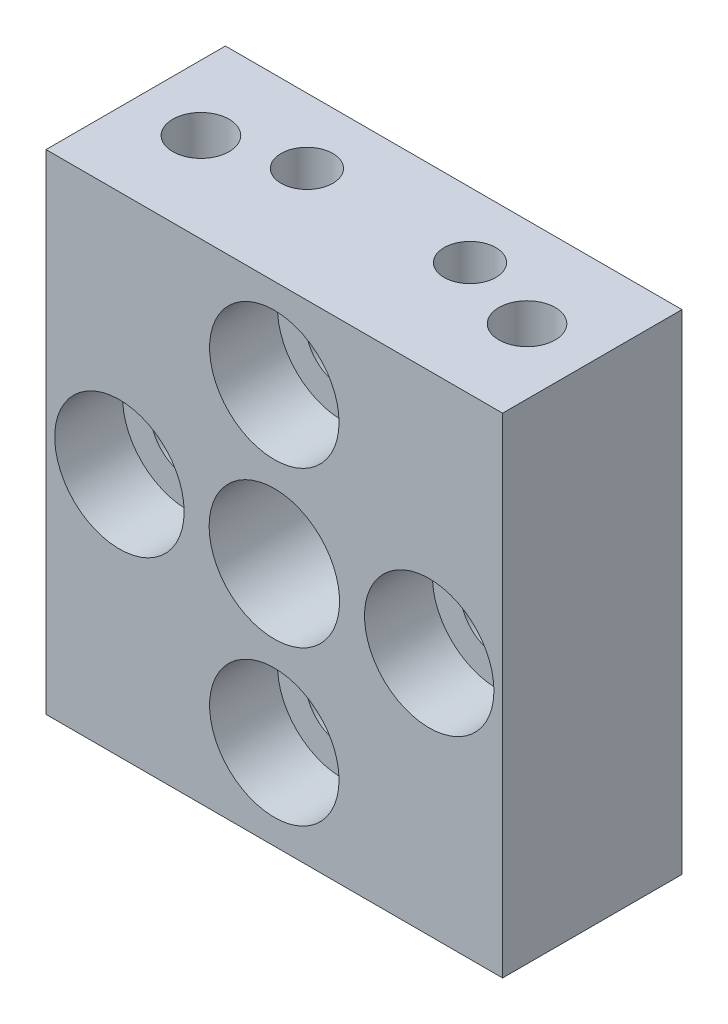
SolidWorks part; units mm, degrees
material "AISI 316 Annealed Stainless Steel Bar (SS)"
ref_plane "Front" through (0, 0, 0) normal (0, 0, 1) x (1, 0, 0)
ref_plane "Top" through (0, 0, 0) normal (0, 1, 0) x (1, 0, 0)
ref_plane "Right" through (0, 0, 0) normal (1, 0, 0) x (0, 0, -1)
sketch "Sketch1" plane through (0, 0, 0) normal (0, 0, 1) x (1, 0, 0)
  line L1 (0, -15) -> (28, -15)
  line L2 (0, -15) -> (0, 15)
  line L3 (0, 15) -> (28, 15)
  line L4 (28, -15) -> (28, 15)
  dimension "D1" = 30
  dimension "D2" = 28
extrude "Boss-Extrude1" add sketch "Sketch1" along normal blind 11
hole_wizard "CBORE for M5 Hex Head Bolt1" positions "Sketch15" profile "Sketch16" counterbore size "M5" standard "ANSI Metric" end condition up to next
sketch "Sketch15" plane through (0, 0, 0) normal (0, 0, 1) x (1, 0, 0)
  line L0 (0, 0) -> (28, 0) construction
  line L1 (0, 15) -> (0, -15) construction
  line L2 (28, -15) -> (28, 15) construction
  point P0 (14, 0)
sketch "Sketch16" plane through (14, 0, 0) normal (1, 0, 0) x (0, 1, 0)
  line L0 (0, 0) -> (0, 11)
  line L1 (0, 11) -> (4, 11)
  line L3 (4, 3.25) -> (4.25, 3)
  line L4 (4.25, 3) -> (5.5, 3)
  line L5 (5.5, 3) -> (5.5, 1)
  line L6 (5.5, 1) -> (6.5, 0)
  line L7 (6.5, 0) -> (0, 0)
  line L8 (-5.5, 1) -> (-6.5, 0) construction
  line L9 (-4, 3.25) -> (-4.25, 3) construction
  line L10 (4, 11) -> (4, 3.25)
  line L11 (0, -6.35) -> (0, 107.95) construction
  dimension "Thru Hole Dia." = 8
  dimension "Thru Hole Depth" = 11
  dimension "C'Bore Dia." = 11
  dimension "C'Bore Depth" = 3
  dimension "Near C'Sink Dia." = 13
  dimension "Near C'Sink Angle" = 90
  dimension "Mid C'Sink Dia." = 8.5
  dimension "Mid C'Sink Angle" = 90
hole_wizard "CBORE for #8 Socket Head Cap Screw3" positions "Sketch17" profile "Sketch18" counterbore size "#8" standard "ANSI Inch" end condition up to next
sketch "Sketch17" plane through (0, 0, 11) normal (0, 0, 1) x (1, 0, 0)
  circle A0 centre (14, 0) radius 9.5
  point P4 (4.5, 0)
  point P6 (14, 9.5)
  point P8 (14, -9.5)
  point P10 (23.5, 0)
  dimension "D1" = 19
sketch "Sketch18" plane through (23.5, 0, 11) normal (1, 0, 0) x (0, -1, 0)
  line L0 (0, 0) -> (0, 11)
  line L1 (0, 11) -> (2.2479, 11)
  line L3 (2.2479, 11) -> (2.2479, 4.1656)
  line L4 (2.2479, 4.1656) -> (3.9687, 4.1656)
  line L5 (3.9687, 4.1656) -> (3.9688, 0)
  line L7 (3.9688, 0) -> (0, 0)
  line L11 (0, -6.35) -> (0, 107.95) construction
  dimension "Thru Hole Dia." = 4.4958
  dimension "Thru Hole Depth" = 11
  dimension "C'Bore Dia." = 7.9375
  dimension "C'Bore Depth" = 4.1656
hole_wizard "#8-32 Tapped Hole1" positions "Sketch11" profile "Sketch13" tap size "#8-32" standard "ANSI Inch"
sketch "Sketch11" plane through (0, 15, 0) normal (0, 1, 0) x (1, 0, 0)
  line L0 (0, -5.5) -> (4, -5.5) construction
  line L1 (0, -11) -> (0, 0) construction
  line L2 (4, -5.5) -> (24, -5.5) construction
  point P0 (4, -5.5)
  point P3 (24, -5.5)
  dimension "D1" = 4
  dimension "D2" = 20
sketch "Sketch13" plane through (4, 15, 5.5) normal (1, 0, 0) x (0, 0, 1)
  line L0 (0, 0) -> (0, 11.0378)
  line L1 (0, 11.0378) -> (1.7272, 10)
  line L2 (1.7272, 10) -> (1.7272, 0)
  line L5 (1.7272, 0) -> (0, 0)
  line L10 (0, 11.0378) -> (-1.7272, 10) construction
  line L11 (0, -6.35) -> (0, 107.95) construction
  dimension "Tap Drill Dia." = 3.4544
  dimension "Tap Drill Depth" = 10
  dimension "Drill Angle" = 118
cosmetic thread "Hole Thread1" parameters "D1"=8, "D2"=4.1656
cosmetic thread "Hole Thread2" parameters "D1"=8, "D2"=4.1656
hole_wizard "1/8 (0.1250) Dowel Hole1" positions "Sketch19" profile "Sketch20" hole size "1/8" standard "ANSI Inch"
sketch "Sketch19" plane through (0, 15, 0) normal (0, 1, 0) x (1, 0, 0)
  line L0 (0, -4) -> (9, -4) construction
  line L2 (9, -4) -> (19, -4) construction
  line L3 (19, -4) -> (28, -4) construction
  line L5 (28, -11) -> (28, 0) construction
  line L6 (0, -11) -> (0, 0) construction
  line L7 (28, 0) -> (0, 0) construction
  point P0 (9, -4)
  point P2 (19, -4)
  dimension "D1" = 10
  dimension "D2" = 4
sketch "Sketch20" plane through (9, 15, 4) normal (1, 0, 0) x (0, 0, 1)
  line L0 (0, 0) -> (0, 5.9539)
  line L1 (0, 5.9539) -> (1.5875, 5)
  line L2 (1.5875, 5) -> (1.5875, 0)
  line L5 (1.5875, 0) -> (0, 0)
  line L10 (0, 5.9539) -> (-1.5875, 5) construction
  line L11 (0, -6.35) -> (0, 107.95) construction
  dimension "Hole Dia." = 3.175
  dimension "Hole Depth" = 5
  dimension "Drill Angle" = 118
mirror "Mirror1" about plane through (0, 0, 0) normal (0, 1, 0) of "1/8 (0.1250) Dowel Hole1", "#8-32 Tapped Hole1"
